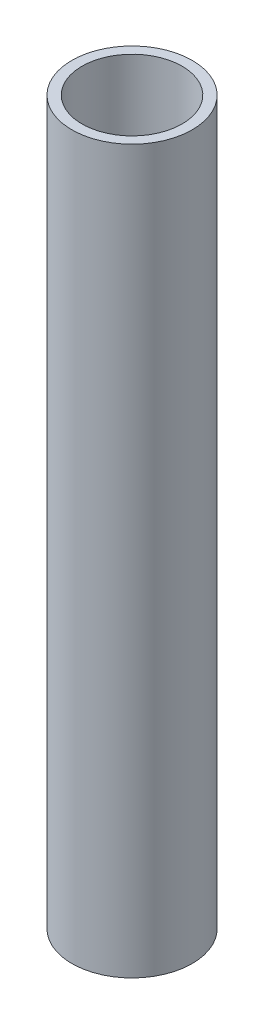
SolidWorks part; units mm, degrees
ref_plane "Front Plane" through (0, 0, 0) normal (0, 0, 1) x (1, 0, 0)
ref_plane "Top Plane" through (0, 0, 0) normal (0, 1, 0) x (1, 0, 0)
ref_plane "Right Plane" through (0, 0, 0) normal (1, 0, 0) x (0, 0, -1)
sketch "Sketch1" plane through (0, 0, 0) normal (1, 0, 0) x (0, 0, -1)
  line L0 (-277.2944, -198.1503) -> (-277.2944, -274.3503)
  dimension "D1" = 76.2
other "Pipe 0.5 SCH 40(1)"
ref_plane "Plane1" through (0, -198.1503, 277.2944) normal (0, -1, 0) x (0, 0, -1)
sketch "Sketch11" plane through (0, -198.1503, 277.2944) normal (0, -1, 0) x (0, 0, -1)
  circle A0 centre (0, 0) radius 5.2832
  circle A1 centre (0, 0) radius 6.35
  point P5 (0, 0)
  dimension "In_dia" = 10.5664
  dimension "Out_dia" = 12.7
